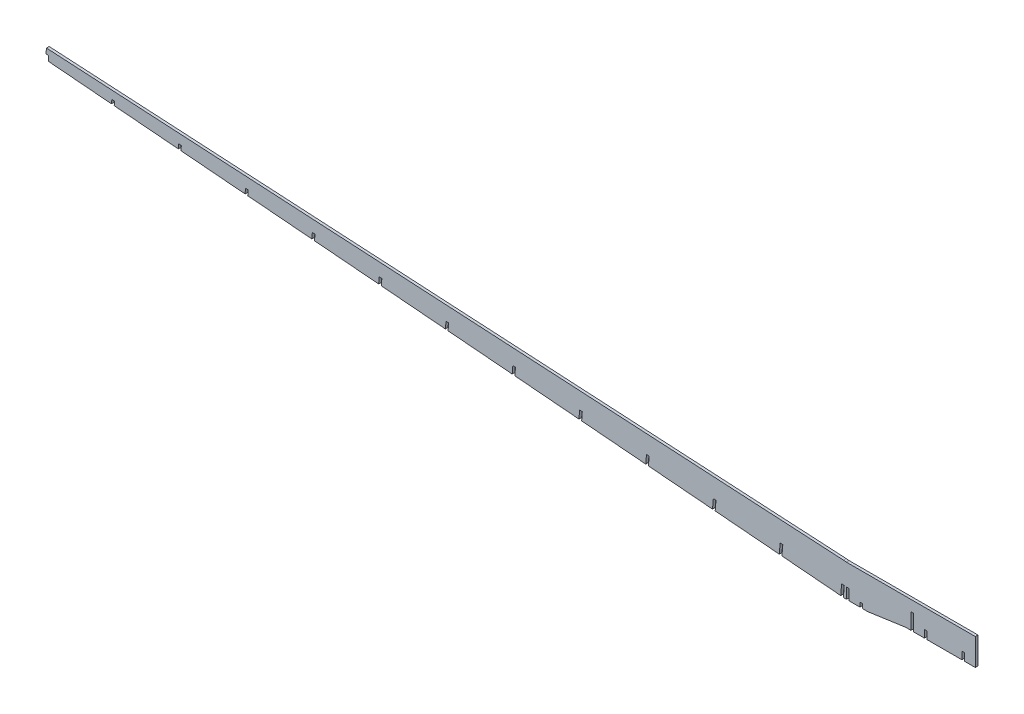
SolidWorks part; units mm, degrees
material "Plywood"
ref_plane "Front Plane" through (0, 0, 0) normal (0, 0, 1) x (1, 0, 0)
ref_plane "Top Plane" through (0, 0, 0) normal (0, 1, 0) x (1, 0, 0)
ref_plane "Right Plane" through (0, 0, 0) normal (1, 0, 0) x (0, 0, -1)
sketch "Sketch1" plane through (0, 0, 0) normal (0, 0, 1) x (1, 0, 0)
  line L0 (76.2, 56.7475) -> (76.2, 37.6975)
  line L1 (79.375, 56.7475) -> (79.375, 37.6975)
  line L2 (0, 44.0475) -> (0, 31.3475)
  line L3 (3.175, 44.0475) -> (3.175, 31.3475)
  line L4 (-5.7133, 44.4467) -> (-6.776, 31.7912)
  line L5 (-2.5494, 44.181) -> (-3.6121, 31.5255)
  line L6 (-1.4923, 31.3475) -> (25.4, 31.3475)
  line L7 (25.4, 31.3475) -> (69.85, 37.6975)
  line L8 (-2.5494, 44.181) -> (-0.424, 69.4919) construction
  line L9 (-0.424, 69.4919) -> (-3.5879, 69.7576)
  line L10 (-3.5879, 69.7576) -> (-5.7133, 44.4467) construction
  line L11 (-5.7133, 44.4467) -> (-2.5494, 44.181)
  line L12 (3.175, 44.0475) -> (3.175, 69.4475) construction
  line L13 (3.175, 69.4475) -> (0, 69.4475)
  line L14 (0, 69.4475) -> (0, 44.0475) construction
  line L15 (0, 44.0475) -> (3.175, 44.0475)
  line L16 (92.075, 37.6975) -> (92.075, 46.5875)
  line L17 (-942.8808, 122.7744) -> (-947.5199, 67.5279)
  line L18 (0, 69.4475) -> (-0.424, 69.4919)
  line L19 (3.175, 69.4475) -> (152.4, 69.4475)
  line L20 (152.4, 69.4475) -> (152.4, 37.6975)
  line L21 (152.4, 37.6975) -> (69.85, 37.6975)
  line L22 (92.075, 46.5875) -> (95.25, 46.5875)
  line L23 (95.25, 46.5875) -> (95.25, 37.6975)
  line L24 (-1.4923, 31.3475) -> (-943.9128, 110.4848)
  line L25 (79.375, 69.4475) -> (79.375, 56.7475)
  line L26 (-942.8808, 122.7744) -> (-3.5879, 69.7576)
  line L27 (136.525, 37.6975) -> (136.525, 46.5875)
  line L28 (76.2, 69.4475) -> (76.2, 56.7475)
  line L29 (79.375, 56.7475) -> (76.2, 56.7475)
  line L30 (-943.5688, 114.5813) -> (-5.7133, 44.4467)
  line L31 (136.525, 46.5875) -> (139.7, 46.5875)
  line L32 (139.7, 46.5875) -> (139.7, 37.6975)
  line L33 (15.875, 31.3475) -> (15.875, 36.4275)
  line L34 (15.875, 36.4275) -> (19.05, 36.4275)
  line L35 (19.05, 36.4275) -> (19.05, 31.3475)
  line L36 (-942.8808, 122.7744) -> (-946.0519, 122.9534)
  line L37 (-946.0519, 122.9534) -> (-946.5835, 116.6233)
  line L38 (-946.5835, 116.6233) -> (-943.4123, 116.4443)
  dimension "D3" = 76.2
  dimension "D10" = 12.3329
  dimension "D11" = 8.2219
  dimension "D2" = 25.4
  dimension "D4" = 25.4
  dimension "D5" = 12.7
  dimension "D7" = 3.175
  dimension "D9" = 3.175
  dimension "D12" = 3.175
  dimension "D6" = 19.05
  dimension "D13" = 6.35
  dimension "D14" = 12.7
  dimension "D16" = 3.175
  dimension "D17" = 3.175
  dimension "D18" = 12.7
  dimension "D19" = 12.7
  dimension "D20" = 8.89
  dimension "D21" = 8.89
  dimension "D15" = 76.2
  dimension "D22" = 12.7
  dimension "D23" = 3.175
  dimension "D24" = 5.08
  dimension "D8" = 6.35
  dimension "D25" = 3.175
  dimension "D26" = 6.35
extrude "Boss-Extrude1" add sketch "Sketch1" along normal mid plane 3.175 contours L17 L30 L11 L5 L24 L6 L2 L15 L3 L7 L21 L0 L28 L19 L13 L18 L9 L26 | L30 L17 L24 L4 | L29 L25 L19 L28 | L19 L25 L1 L21 L20 | L37 L38 L17 L36
sketch "Sketch2" plane through (0, 0, 1.5875) normal (0, 0, 1) x (1, 0, 0)
  line L2 (-73.2652, 73.2231) -> (-80.3969, -11.7061)
  line L3 (-943.5688, 114.5813) -> (-5.7133, 44.4467)
  line L6 (-76.4291, 73.4888) -> (-83.5608, -11.4404)
  line L7 (-6.776, 31.7912) -> (-943.9128, 110.4848)
  line L10 (-152.4177, 77.6821) -> (-159.3225, -4.5442)
  line L14 (-155.5816, 77.9478) -> (-162.4863, -4.2785)
  line L18 (-231.5658, 82.1932) -> (-238.251, 2.5812)
  line L22 (-234.7297, 82.4589) -> (-241.4149, 2.8469)
  line L26 (-310.7178, 86.6582) -> (-317.1769, 9.7387)
  line L30 (-313.8817, 86.9239) -> (-320.3408, 10.0043)
  line L34 (-389.8657, 91.1713) -> (-396.1056, 16.8623)
  line L38 (-393.0296, 91.437) -> (-399.2695, 17.128)
  line L42 (-469.0186, 95.6263) -> (-475.031, 24.0265)
  line L46 (-472.1824, 95.892) -> (-478.1948, 24.2921)
  line L50 (-548.1666, 100.1381) -> (-553.9596, 31.1506)
  line L54 (-551.3305, 100.4038) -> (-557.1235, 31.4163)
  line L58 (-627.3195, 104.5918) -> (-632.8849, 38.3152)
  line L62 (-630.4834, 104.8575) -> (-636.0488, 38.5809)
  line L66 (-706.4673, 109.1069) -> (-711.8138, 45.4365)
  line L70 (-709.6312, 109.3725) -> (-714.9777, 45.7022)
  line L74 (-785.6206, 113.5558) -> (-790.7389, 52.6041)
  line L78 (-788.7845, 113.8214) -> (-793.9027, 52.8697)
  line L82 (-864.7684, 118.071) -> (-869.6679, 59.7246)
  line L86 (-867.9323, 118.3366) -> (-872.8317, 59.9902)
  line L89 (-942.9091, 122.4365) -> (-947.5795, 66.8182)
  line M2 (-943.9128, 110.4848) -> (-6.776, 31.7912)
extrude "Cut-Extrude1" cut sketch "Sketch2" against normal through all contours L3 L6 L2 M2 | L3 L14 L7 L10 | L3 L22 L7 L18 | L3 L30 L7 L26 | L3 L38 L7 L34 | L3 L46 L7 L42 | L3 L54 L7 L50 | L3 L62 L7 L58 | L3 L70 L7 L66 | L3 L78 L7 L74 | L3 L86 L7 L82
move or copy body "Body-Move/Copy1" [suppressed] bodies to move or copy 102 parameters "D1"=0, "D2"=0, "D3"=0
equation "\"D11@Sketch1\"=\"D10@Sketch1\"*(2/3)"
